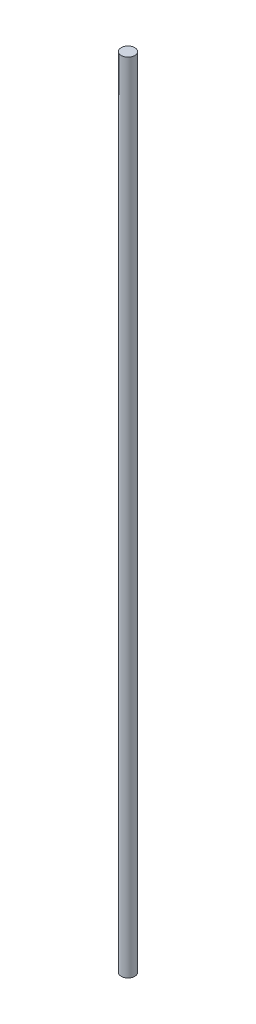
SolidWorks part; units mm, degrees
ref_plane "Front Plane" through (0, 0, 0) normal (0, 0, 1) x (1, 0, 0)
ref_plane "Top Plane" through (0, 0, 0) normal (0, 1, 0) x (1, 0, 0)
ref_plane "Right Plane" through (0, 0, 0) normal (1, 0, 0) x (0, 0, -1)
sketch "Sketch1" plane through (0, 0, 0) normal (0, 1, 0) x (1, 0, 0)
  circle A0 centre (0, 0) radius 0.855
  dimension "D1" = 1.71
extrude "Boss-Extrude1" add sketch "Sketch1" along normal mid plane 100
